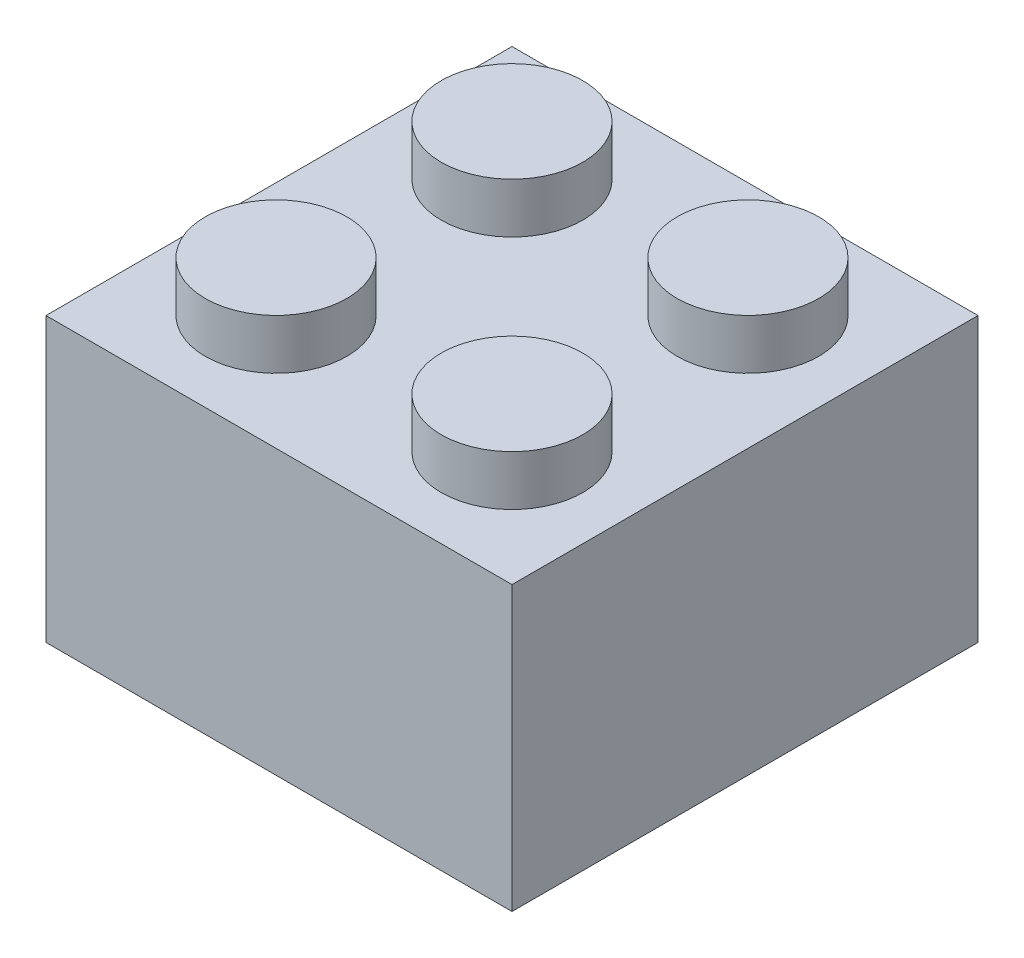
SolidWorks part; units mm, degrees
ref_plane "Спереди" through (0, 0, 0) normal (0, 0, 1) x (1, 0, 0)
ref_plane "Сверху" through (0, 0, 0) normal (0, 1, 0) x (1, 0, 0)
ref_plane "Справа" through (0, 0, 0) normal (1, 0, 0) x (0, 0, -1)
sketch "Эскиз1" plane through (0, 0, 0) normal (0, 1, 0) x (1, 0, 0)
  line L1 (0, 0) -> (15.8, 0)
  line L2 (0, 0) -> (0, 15.8)
  line L3 (0, 15.8) -> (15.8, 15.8)
  line L4 (15.8, 0) -> (15.8, 15.8)
  dimension "D1" = 15.8
  dimension "D2" = 15.8
extrude "Бобышка-Вытянуть1" add sketch "Эскиз1" along normal blind 9.6 contours L2 L1 L4 L3
sketch "Эскиз2" plane through (0, 9.6, 0) normal (0, 1, 0) x (1, 0, 0)
  line L0 (0, 15.8) -> (15.8, 15.8) construction
  line L1 (0, 0) -> (0, 15.8) construction
  circle A0 centre (3.9, 11.9) radius 2.4
  circle A1 centre (11.9, 11.9) radius 2.4
  circle A2 centre (11.9, 3.9) radius 2.4
  circle A3 centre (3.9, 3.9) radius 2.4
  dimension "D1" = 4.8
  dimension "D2" = 3.9
  dimension "D3" = 3.9
  dimension "D4" = 2
  dimension "D5" = 2
extrude "Бобышка-Вытянуть2" add sketch "Эскиз2" along normal blind 1.7
sketch "Эскиз3" plane through (0, 0, 0) normal (0, -1, 0) x (1, 0, 0)
  line L0 (0, 0) -> (15.8, 0) construction
  line L1 (15.8, 0) -> (15.8, -15.8) construction
  circle A0 centre (11.9, -3.9) radius 2.5
  circle A1 centre (3.9, -3.9) radius 2.5
  circle A2 centre (3.9, -11.9) radius 2.5
  circle A3 centre (11.9, -11.9) radius 2.5
  dimension "D1" = 5
  dimension "D2" = 3.9
  dimension "D3" = 3.9
  dimension "D4" = 2
  dimension "D5" = 2
extrude "Вырез-Вытянуть2" cut sketch "Эскиз3" against normal blind 1.8
